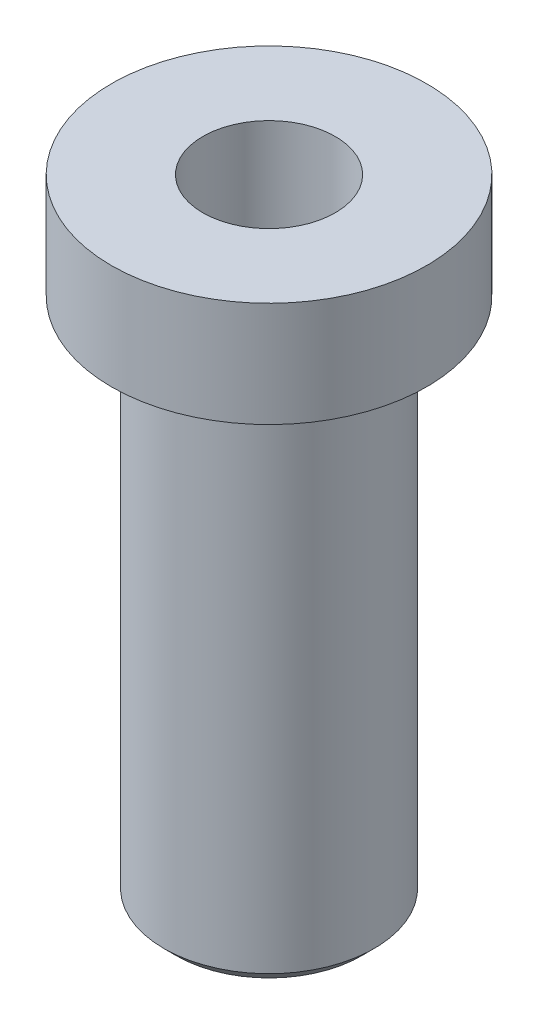
SolidWorks part; units mm, degrees
ref_plane "Front Plane" through (0, 0, 0) normal (0, 0, 1) x (1, 0, 0)
ref_plane "Top Plane" through (0, 0, 0) normal (0, 1, 0) x (1, 0, 0)
ref_plane "Right Plane" through (0, 0, 0) normal (1, 0, 0) x (0, 0, -1)
sketch "Sketch1" plane through (0, 0, 0) normal (0, 1, 0) x (1, 0, 0)
  circle A0 centre (0, 0) radius 0.5
  dimension "D1" = 1
extrude "Boss-Extrude1" add sketch "Sketch1" along normal blind 3
sketch "Sketch2" plane through (0, 3, 0) normal (0, 1, 0) x (1, 0, 0)
  circle A0 centre (0, 0) radius 0.75
  dimension "D1" = 1.5
extrude "Boss-Extrude2" add sketch "Sketch2" against normal blind 0.5
chamfer "Chamfer1" distance 0.06 angle 45 1 edges at (0, 0, 0.5)
sketch "Sketch3" plane through (0, 0, 0) normal (0, 1, 0) x (1, 0, 0)
  circle A0 centre (0, 0) radius 0.315
  dimension "D1" = 0.63
extrude "Cut-Extrude1" cut sketch "Sketch3" against normal through all from surface at 3 starting at face at (0, 3, 0.75)
